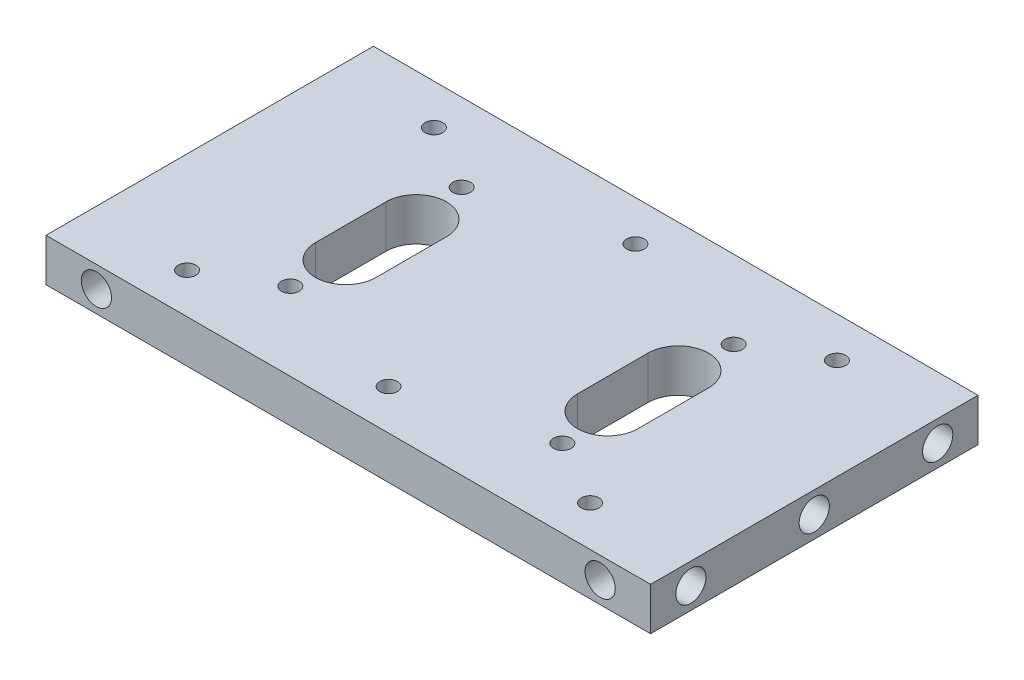
SolidWorks part; units mm, degrees
ref_plane "Front Plane" through (0, 0, 0) normal (0, 0, 1) x (1, 0, 0)
ref_plane "Top Plane" through (0, 0, 0) normal (0, 1, 0) x (1, 0, 0)
ref_plane "Right Plane" through (0, 0, 0) normal (1, 0, 0) x (0, 0, -1)
sketch "Sketch1" plane through (0, 0, 0) normal (1, 0, 0) x (0, 0, -1)
  line L1 (-32.5, -4.25) -> (32.5, -4.25)
  line L2 (-32.5, -4.25) -> (-32.5, 4.25)
  line L3 (-32.5, 4.25) -> (32.5, 4.25)
  line L4 (32.5, -4.25) -> (32.5, 4.25)
  line L5 (-32.5, -4.25) -> (32.5, 4.25) construction
  line L6 (-32.5, 4.25) -> (32.5, -4.25) construction
  point P0 (0, 0)
  dimension "D1" = 8.5
  dimension "D2" = 65
extrude "Boss-Extrude1" add sketch "Sketch1" along normal blind 120
hole_wizard "Ø6.0mm Dowel Hole1" positions "Sketch2" profile "Sketch3" hole size "Ø6.0" standard "ANSI Metric"
sketch "Sketch2" plane through (120, 0, 0) normal (1, 0, 0) x (0, 0, -1)
  line L0 (-32.5, 4.25) -> (-32.5, -4.25) construction
  line L1 (32.5, -4.25) -> (32.5, 4.25) construction
  point P0 (-24.5, 0)
  point P2 (0, 0)
  point P5 (24.5, 0)
  dimension "D1" = 8
  dimension "D2" = 8
sketch "Sketch3" plane through (120, 0, 24.5) normal (0, 1, 0) x (0, 0, -1)
  line L0 (0, 0) -> (0, 11.8026)
  line L1 (0, 11.8026) -> (3, 10)
  line L2 (3, 10) -> (3, 0)
  line L5 (3, 0) -> (0, 0)
  line L10 (0, 11.8026) -> (-3, 10) construction
  line L11 (0, -6.35) -> (0, 107.95) construction
  dimension "Hole Dia." = 6
  dimension "Hole Depth" = 10
  dimension "Drill Angle" = 118
ref_plane "Plane1" through (60, 0, 0) normal (1, 0, 0) x (0, 0, -1)
mirror "Mirror1" about plane through (60, 0, 0) normal (1, 0, 0) of "Ø6.0mm Dowel Hole1"
hole_wizard "Ø6.0mm Dowel Hole2" positions "Sketch4" profile "Sketch5" hole size "Ø6.0" standard "ANSI Metric"
sketch "Sketch4" plane through (0, 0, -32.5) normal (0, 0, -1) x (-1, 0, 0)
  line L0 (-120, -4.25) -> (-120, 4.25) construction
  line L1 (0, -4.25) -> (0, 4.25) construction
  line L2 (-120, 0) -> (0, 0) construction
  point P0 (-110, 0)
  point P2 (-10, 0)
  dimension "D1" = 10
  dimension "D2" = 10
sketch "Sketch5" plane through (110, 0, -32.5) normal (1, 0, 0) x (0, 1, 0)
  line L0 (0, 0) -> (0, 9.8026)
  line L1 (0, 9.8026) -> (3, 8)
  line L2 (3, 8) -> (3, 0)
  line L5 (3, 0) -> (0, 0)
  line L10 (0, 9.8026) -> (-3, 8) construction
  line L11 (0, -6.35) -> (0, 107.95) construction
  dimension "Hole Dia." = 6
  dimension "Hole Depth" = 8
  dimension "Drill Angle" = 118
mirror "Mirror2" about plane through (0, 0, 0) normal (0, 0, 1) of "Ø6.0mm Dowel Hole2"
sketch "Sketch6" plane through (0, 4.25, 0) normal (0, 1, 0) x (1, 0, 0)
  line L0 (86, -7) -> (86, 7) construction
  line L1 (80, -7) -> (80, 7)
  line L2 (92, -7) -> (92, 7)
  line L3 (120, 32.5) -> (120, -32.5) construction
  arc A0 (80, -7) -> (92, -7) centre (86, -7) ccw
  arc A1 (92, 7) -> (80, 7) centre (86, 7) ccw
  point P2 (86, 0)
  point P10 (120, 0)
  dimension "D3" = 12
  dimension "D1" = 40
  dimension "D2" = 14
extrude "Cut-Extrude1" cut sketch "Sketch6" against normal through all
mirror "Mirror3" about plane through (60, 0, 0) normal (1, 0, 0) of "Cut-Extrude1"
sketch "Sketch7" plane through (0, 4.25, 0) normal (0, 1, 0) x (1, 0, 0)
  line L0 (120, 32.5) -> (0, 32.5) construction
  line L1 (87, 17) -> (33, 17)
  line L2 (87, 17) -> (87, -17)
  line L3 (87, -17) -> (33, -17)
  line L4 (33, 17) -> (33, -17)
  line L5 (87, 17) -> (33, -17) construction
  line L6 (87, -17) -> (33, 17) construction
  point P0 (60, 0)
  point P8 (60, 32.5)
  dimension "D1" = 54
  dimension "D2" = 34
hole_wizard "Ø3.0mm Dowel Hole1" positions "Sketch8" profile "Sketch9" hole size "Ø3.0" standard "ANSI Metric" end condition through all
sketch "Sketch8" plane through (0, 4.25, 0) normal (0, 1, 0) x (1, 0, 0)
  line L0 (120, -32.5) -> (0, -32.5) construction
  line L1 (120, 32.5) -> (0, 32.5) construction
  line L2 (120, 32.5) -> (120, -32.5) construction
  line L3 (0, 32.5) -> (0, -32.5) construction
  point P0 (87, -17)
  point P3 (87, 17)
  point P6 (33, 17)
  point P9 (33, -17)
  point P13 (100, -24.5)
  point P15 (60, -24.5)
  point P17 (20, -24.5)
  point P19 (100, 24.5)
  point P21 (60, 24.5)
  point P23 (20, 24.5)
  point P40 (60, 32.5)
  dimension "D1" = 8
  dimension "D2" = 8
  dimension "D3" = 20
  dimension "D4" = 20
sketch "Sketch9" plane through (87, 4.25, 17) normal (1, 0, 0) x (0, 0, 1)
  line L0 (0, 0) -> (0, 8.5)
  line L1 (0, 8.5) -> (1.75, 8.5)
  line L2 (1.75, 8.5) -> (1.75, 0)
  line L5 (1.75, 0) -> (0, 0)
  line L11 (0, -6.35) -> (0, 107.95) construction
  dimension "Thru Hole Dia." = 3.5
  dimension "Thru Hole Depth" = 8.5
